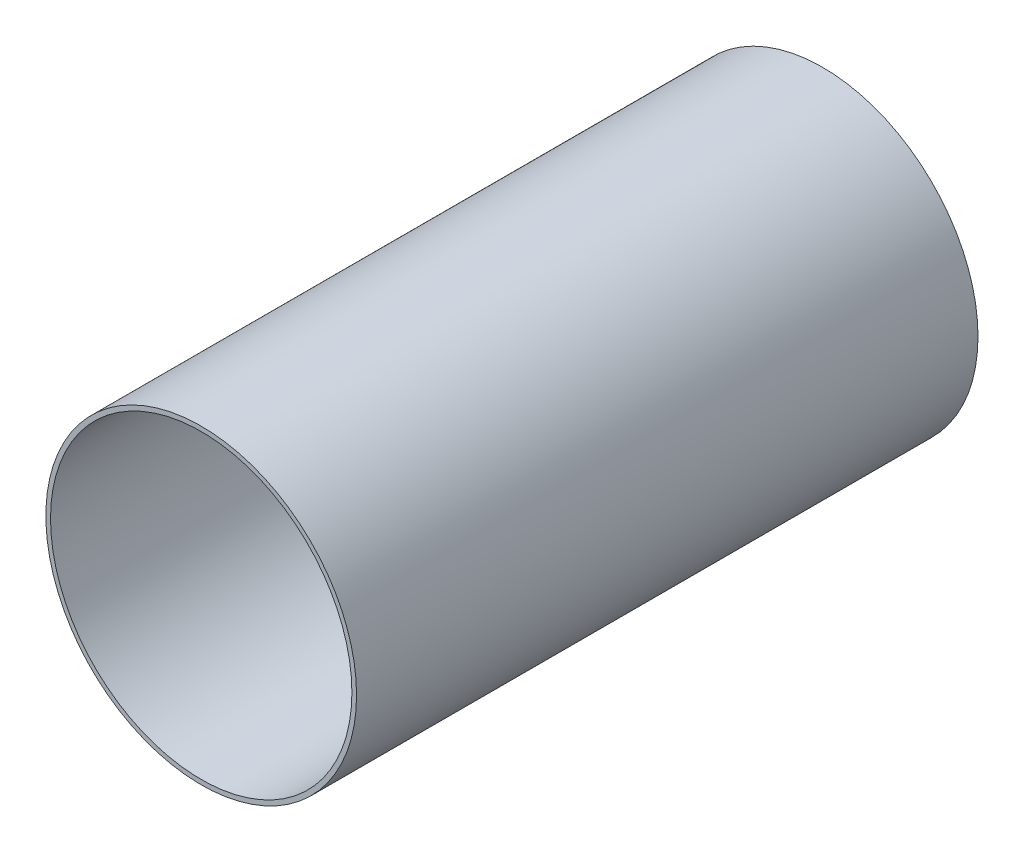
SolidWorks part; units mm, degrees
material "S-Glass Fiber"
ref_plane "Front Plane" through (0, 0, 0) normal (0, 0, 1) x (1, 0, 0)
ref_plane "Top Plane" through (0, 0, 0) normal (0, 1, 0) x (1, 0, 0)
ref_plane "Right Plane" through (0, 0, 0) normal (1, 0, 0) x (0, 0, -1)
sketch "Sketch1" plane through (0, 0, 0) normal (0, 0, 1) x (1, 0, 0)
  circle A0 centre (0, 0) radius 76.2
  circle A1 centre (0, 0) radius 73.914
  dimension "D1" = 152.4
  dimension "D2" = 147.828
extrude "Boss-Extrude1" add sketch "Sketch1" along normal blind 304.8
